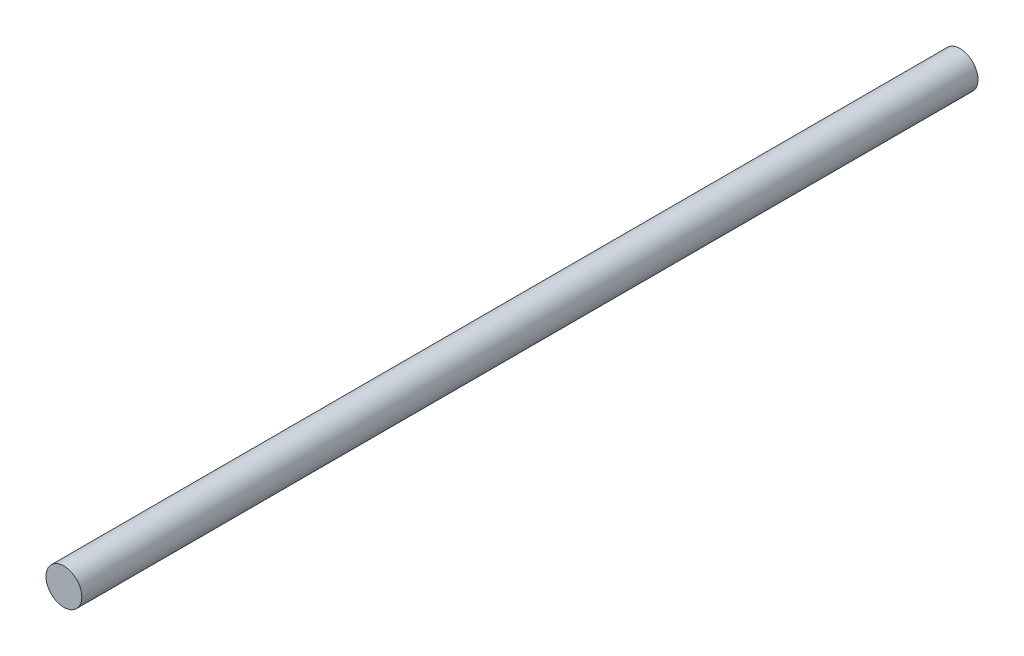
SolidWorks part; units mm, degrees
ref_plane "Ebene vorne" through (0, 0, 0) normal (0, 0, 1) x (1, 0, 0)
ref_plane "Ebene oben" through (0, 0, 0) normal (0, 1, 0) x (1, 0, 0)
ref_plane "Ebene rechts" through (0, 0, 0) normal (1, 0, 0) x (0, 0, -1)
sketch "Skizze1" plane through (0, 0, 0) normal (0, 0, 1) x (1, 0, 0)
  circle A0 centre (0, 0) radius 6
  dimension "D1" = 12
extrude "Aufsatz-Linear austragen1" add sketch "Skizze1" along normal blind 300
ref_point "Punkt1"
